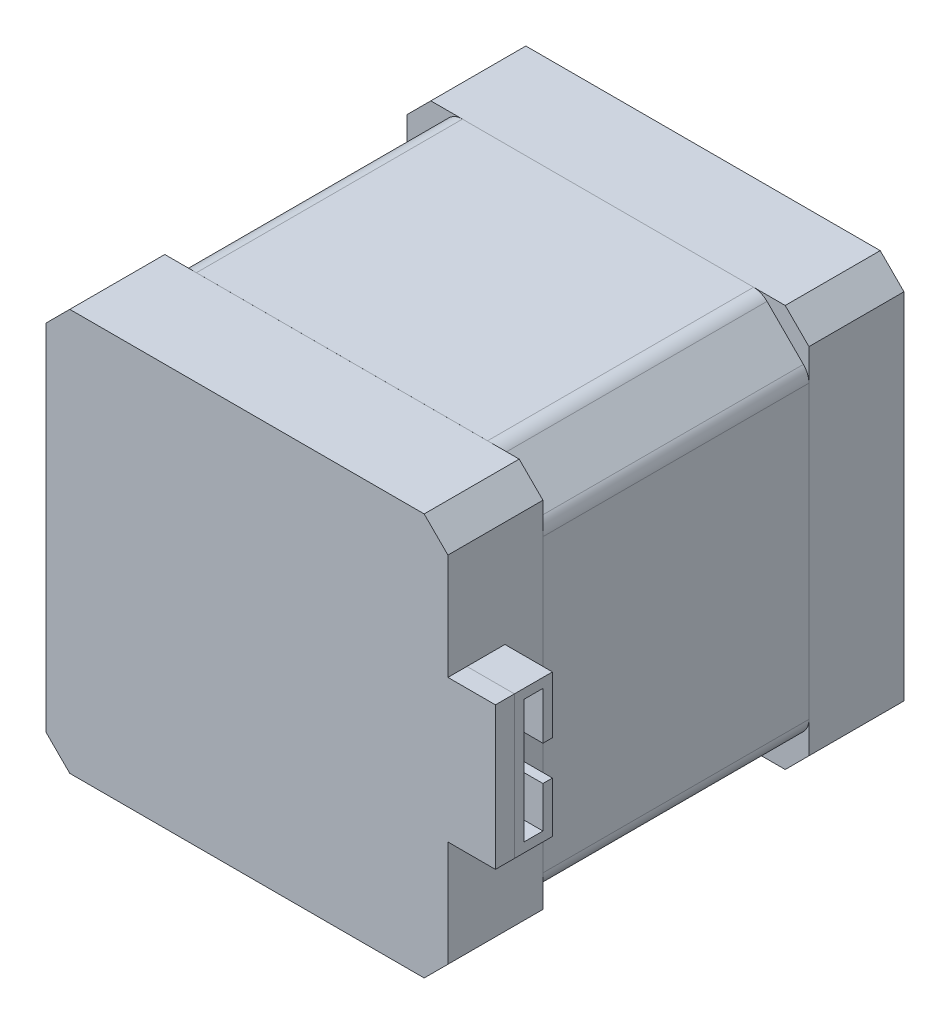
SolidWorks part; units mm, degrees
ref_plane "Alzado" through (0, 0, 0) normal (0, 0, 1) x (1, 0, 0)
ref_plane "Planta" through (0, 0, 0) normal (0, 1, 0) x (1, 0, 0)
ref_plane "Vista lateral" through (0, 0, 0) normal (1, 0, 0) x (0, 0, -1)
sketch "Sketch1" plane through (0, 0, 0) normal (0, 0, 1) x (1, 0, 0)
  line L1 (-21.3978, 24.074) -> (20.9022, 24.074)
  line L2 (-21.3978, 24.074) -> (-21.3978, -18.226)
  line L3 (-21.3978, -18.226) -> (20.9022, -18.226)
  line L4 (20.9022, 24.074) -> (20.9022, -18.226)
  dimension "D1" = 42.3
  dimension "D2" = 42.3
extrude "Boss-Extrude2" add sketch "Sketch1" along normal blind 10
sketch "Sketch2" plane through (0, 0, 10) normal (0, 0, 1) x (1, 0, 0)
  line L1 (-21.3978, 24.074) -> (20.9022, 24.074)
  line L2 (-21.3978, 24.074) -> (-21.3978, -18.226)
  line L3 (-21.3978, -18.226) -> (20.9022, -18.226)
  line L4 (20.9022, 24.074) -> (20.9022, -18.226)
extrude "Boss-Extrude3" add sketch "Sketch2" along normal blind 28 separate body
chamfer "Chamfer1" distance 5 angle 45 4 edges at (20.9022, -18.226, 24) (-21.3978, -18.226, 24) (-21.3978, 24.074, 24) (20.9022, 24.074, 24)
fillet "Fillet1" radius 2 8 edges at (-21.3978, -13.226, 24) (-16.3978, -18.226, 24) (15.9022, -18.226, 24) (20.9022, -13.226, 24) (20.9022, 19.074, 24) (15.9022, 24.074, 24) (-16.3978, 24.074, 24) (-21.3978, 19.074, 24)
chamfer "Chamfer2" distance 2.5 angle 45 4 edges at (-21.3978, -18.226, 5) (-21.3978, 24.074, 5) (20.9022, -18.226, 5) (20.9022, 24.074, 5)
sketch "Sketch4" plane through (0, 0, 38) normal (0, 0, 1) x (1, 0, 0)
  line L0 (-21.3978, 21.574) -> (-21.3978, 24.072) construction
  line L1 (-21.3978, 24.072) -> (-18.8978, 24.074) construction
  line L3 (-21.3978, 24.072) -> (20.9022, 24.072)
  line L4 (-21.3978, 24.072) -> (-21.3978, -18.228)
  line L5 (-21.3978, -18.228) -> (20.9022, -18.228)
  line L6 (20.9022, 24.072) -> (20.9022, -18.228)
  dimension "D1" = 42.3
  dimension "D2" = 42.3
extrude "Boss-Extrude4" add sketch "Sketch4" along normal blind 10 separate body
chamfer "Chamfer3" distance 2.5 angle 45 4 edges at (-21.3978, -18.228, 43) (20.9022, -18.228, 43) (20.9022, 24.072, 43) (-21.3978, 24.072, 43)
sketch "Sketch5" plane through (0, 0, 0) normal (0, 0, -1) x (-1, 0, 0)
  line L0 (-20.9022, -15.726) -> (-20.9022, 21.574) construction
  line L1 (-18.4022, 24.074) -> (18.8978, 24.074) construction
  circle A0 centre (0.2478, 2.924) radius 11
  dimension "D1" = 22
  dimension "D2" = 21.15
  dimension "D3" = 21.15
extrude "Boss-Extrude5" add sketch "Sketch5" along normal blind 2
sketch "Sketch6" plane through (0, 0, -2) normal (0, 0, -1) x (-1, 0, 0)
  circle A0 centre (0.2478, 2.924) radius 4
  dimension "D1" = 8
extrude "Cut-Extrude1" cut sketch "Sketch6" against normal blind 2
sketch "Sketch7" plane through (0, 0, 0) normal (0, 0, -1) x (-1, 0, 0)
  circle A0 centre (0.2478, 2.924) radius 2.5
  point P3 (-47.6546, -3.2418)
  dimension "D1" = 5
extrude "Cut-Extrude2" cut sketch "Sketch7" against normal blind 1
sketch "Sketch11" plane through (0, 0, 0) normal (0, 0, -1) x (-1, 0, 0)
  line L0 (-18.4022, 24.074) -> (18.8978, 24.074) construction
  line L1 (21.3978, 21.574) -> (21.3978, -15.726) construction
  circle A0 centre (-15.2522, 18.424) radius 1.5
  circle A1 centre (15.7478, 18.424) radius 1.5
  circle A2 centre (15.7478, -12.576) radius 1.5
  circle A3 centre (-15.2522, -12.576) radius 1.5
  dimension "D1" = 3
  dimension "D2" = 31
  dimension "D3" = 31
  dimension "D4" = 31
  dimension "D5" = 31
  dimension "D6" = 5.65
  dimension "D7" = 5.65
  dimension "D8" = 31
extrude "Cut-Extrude3" cut sketch "Sketch11" against normal blind 2.5
sketch "Sketch12" plane through (20.9022, 0, 0) normal (1, 0, 0) x (0, 0, -1)
  line L0 (-48, -15.728) -> (-48, 21.572) construction
  line L1 (-48, 10.422) -> (-46, 10.422)
  line L2 (-48, 10.422) -> (-48, -4.578)
  line L3 (-48, -4.578) -> (-46, -4.578)
  line L4 (-46, 10.422) -> (-46, -4.578)
  dimension "D1" = 15
  dimension "D2" = 2
  dimension "D3" = 11.15
extrude "Boss-Extrude6" add sketch "Sketch12" along normal blind 5
sketch "Sketch13" plane through (20.9022, 0, 0) normal (1, 0, 0) x (0, 0, -1)
  line L0 (-46, 10.422) -> (-42, 10.422)
  line L1 (-42, 10.422) -> (-42, 4.422)
  line L2 (-42, 4.422) -> (-43, 4.422)
  line L3 (-43, 4.422) -> (-43, 9.422)
  line L4 (-43, 9.422) -> (-45, 9.422)
  line L5 (-45, 9.422) -> (-45, -3.578)
  line L6 (-45, -3.578) -> (-43, -3.578)
  line L7 (-43, -3.578) -> (-43, 0.75)
  line L8 (-43, 0.75) -> (-42, 0.75)
  line L11 (-46, -4.578) -> (-46, 10.422)
  line L12 (-46, -4.578) -> (-42, -4.578)
  line L13 (-42, -4.578) -> (-42, 0.75)
  dimension "D1" = 4
  dimension "D3" = 6
  dimension "D5" = 1
  dimension "D6" = 1
  dimension "D7" = 1
  dimension "D8" = 1
  dimension "D9" = 13
extrude "Boss-Extrude7" add sketch "Sketch13" along normal blind 5 separate body
